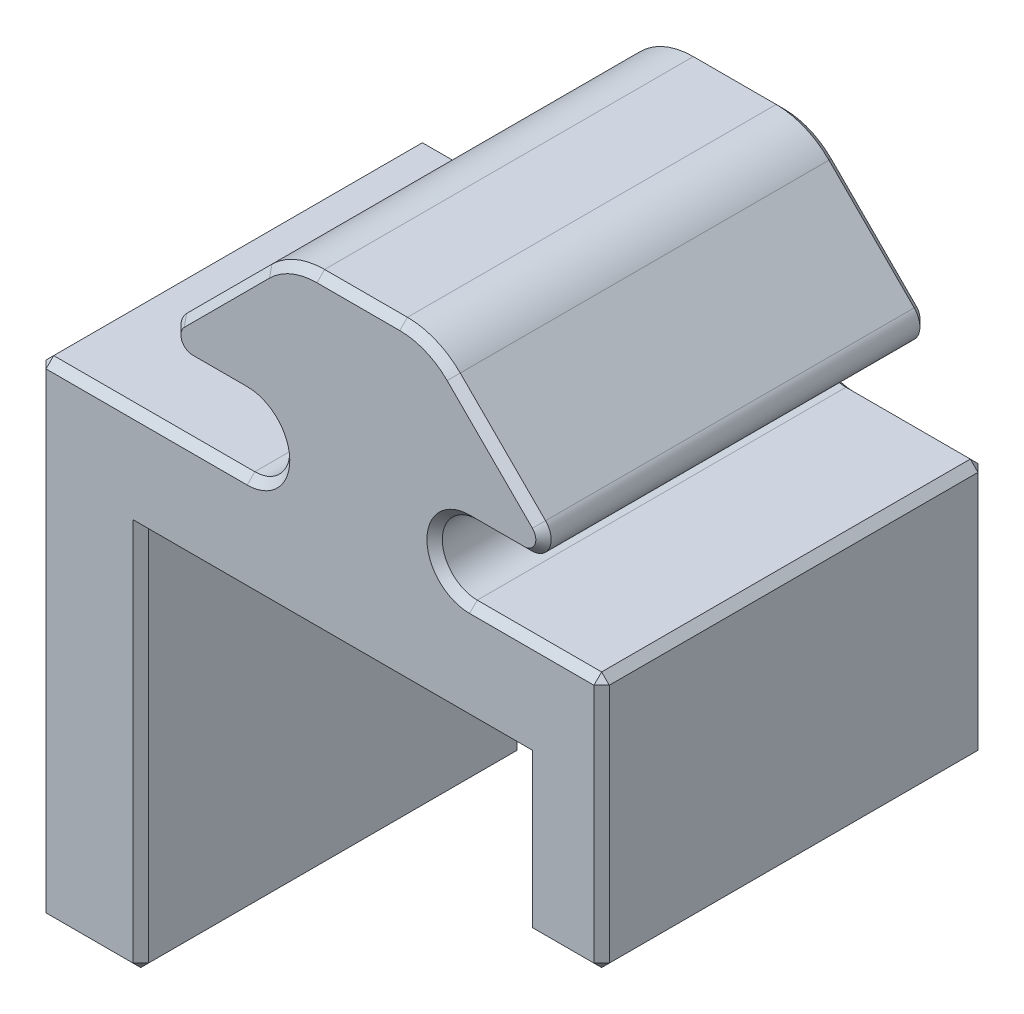
SolidWorks part; units mm, degrees
ref_plane "Front Plane" through (0, 0, 0) normal (0, 0, 1) x (1, 0, 0)
ref_plane "Top Plane" through (0, 0, 0) normal (0, 1, 0) x (1, 0, 0)
ref_plane "Right Plane" through (0, 0, 0) normal (1, 0, 0) x (0, 0, -1)
sketch "Sketch1" plane through (0, 0, 0) normal (0, 0, 1) x (1, 0, 0)
  line L0 (-5.3171, -3.1021) -> (-5.3171, -5.1021) construction
  line L1 (-5.3171, -5.1021) -> (5.3171, -5.1021) construction
  line L2 (5.3171, -5.1021) -> (5.3171, -3.1021) construction
  line L13 (-5.3171, -3.1021) -> (-4.3434, -3.1021) construction
  line L14 (-4.3434, -0.8923) -> (-6.4748, -0.8923) construction
  line L15 (-7.1932, 0.8421) -> (-3.8632, 4.1722) construction
  line L16 (-1.6181, 5.1021) -> (1.6181, 5.1021) construction
  line L17 (3.8632, 4.1722) -> (7.1932, 0.8421) construction
  line L18 (6.4748, -0.8923) -> (4.3434, -0.8923) construction
  line L19 (4.3434, -3.1021) -> (5.3171, -3.1021) construction
  line L20 (-5.0571, -3.3621) -> (-5.0571, -4.8421) construction
  line L21 (-5.0571, -4.8421) -> (5.0571, -4.8421) construction
  line L22 (5.0571, -4.8421) -> (5.0571, -3.3621) construction
  line L23 (4.3434, -3.3621) -> (5.0571, -3.3621)
  line L24 (6.4748, -0.6323) -> (4.3434, -0.6323)
  line L25 (3.6793, 3.9883) -> (7.0094, 0.6583)
  line L26 (-1.6181, 4.8421) -> (1.6181, 4.8421)
  line L27 (-7.0094, 0.6583) -> (-3.6793, 3.9883)
  line L28 (-4.3434, -0.6323) -> (-6.4748, -0.6323)
  line L29 (-5.0571, -3.3621) -> (-4.3434, -3.3621)
  line L30 (-5.0571, -3.3621) -> (-12.5, -3.3621)
  line L31 (-12.5, -3.3621) -> (-12.5, -7.3621)
  line L32 (-12.5, -7.3621) -> (9.5, -7.3621)
  line L33 (9.5, -7.3621) -> (9.5, -3.3621)
  line L34 (9.5, -3.3621) -> (5.0571, -3.3621)
  arc A6 (-4.3434, -3.1021) -> (-4.3434, -0.8923) centre (-4.3434, -1.9972) ccw construction
  arc A7 (-7.1932, 0.8421) -> (-6.4748, -0.8923) centre (-6.4748, 0.1237) ccw construction
  arc A8 (-1.6181, 5.1021) -> (-3.8632, 4.1722) centre (-1.6181, 1.9271) ccw construction
  arc A9 (3.8632, 4.1722) -> (1.6181, 5.1021) centre (1.6181, 1.9271) ccw construction
  arc A10 (6.4748, -0.8923) -> (7.1932, 0.8421) centre (6.4748, 0.1237) ccw construction
  arc A11 (4.3434, -0.8923) -> (4.3434, -3.1021) centre (4.3434, -1.9972) ccw construction
  arc A12 (4.3434, -0.6323) -> (4.3434, -3.3621) centre (4.3434, -1.9972) ccw
  arc A13 (6.4748, -0.6323) -> (7.0094, 0.6583) centre (6.4748, 0.1237) ccw
  arc A14 (3.6793, 3.9883) -> (1.6181, 4.8421) centre (1.6181, 1.9271) ccw
  arc A15 (-1.6181, 4.8421) -> (-3.6793, 3.9883) centre (-1.6181, 1.9271) ccw
  arc A16 (-7.0094, 0.6583) -> (-6.4748, -0.6323) centre (-6.4748, 0.1237) ccw
  arc A17 (-4.3434, -3.3621) -> (-4.3434, -0.6323) centre (-4.3434, -1.9972) ccw
  dimension "D1" = 0.26
  dimension "D2" = 4
  dimension "D3" = 12.5
  dimension "D4" = 22
extrude "Boss-Extrude1" add sketch "Sketch1" along normal blind 15
sketch "Sketch2" plane through (0, -7.3621, 0) normal (0, -1, 0) x (1, 0, 0)
  line L0 (-12.5, 15) -> (9.5, 15) construction
  line L1 (-12.5, 0) -> (-8.5, 0)
  line L2 (-12.5, 0) -> (-12.5, 15)
  line L3 (-12.5, 15) -> (-8.5, 15)
  line L4 (-8.5, 0) -> (-8.5, 15)
  dimension "D1" = 4
extrude "Boss-Extrude2" add sketch "Sketch2" along normal blind 15
sketch "Sketch3" plane through (0, -7.3621, 0) normal (0, -1, 0) x (1, 0, 0)
  line L0 (-8.5, 0) -> (9.5, 0) construction
  line L1 (9.5, 15) -> (6.5, 15)
  line L2 (9.5, 15) -> (9.5, 0)
  line L3 (9.5, 0) -> (6.5, 0)
  line L4 (6.5, 15) -> (6.5, 0)
  line L6 (-8.5, 0) -> (-8.5, 15) construction
  dimension "D1" = 15
extrude "Boss-Extrude3" add sketch "Sketch3" along normal blind 6
chamfer "Chamfer1" distance 0.3 angle 45 46 edges at (-10.5, -22.3621, 0) (-8.5, -14.8621, 0) (-1, -7.3621, 0) (6.5, -10.3621, 0) (8, -13.3621, 0) (9.5, -8.3621, 0) (6.9217, -3.3621, 0) (2.9785, -1.9972, 0) (5.4091, -0.6323, 0) (7.1732, -0.1656, 0) (5.3443, 2.3233, 0) (2.7336, 4.6202, 0) (0, 4.8421, 0) (-2.7336, 4.6202, 0) (-5.3443, 2.3233, 0) (-7.1732, -0.1656, 0) (-5.4091, -0.6323, 0) (-2.9785, -1.9972, 0) (-8.4217, -3.3621, 0) (-12.5, -12.8621, 0) (-2.9785, -1.9972, 15) (-5.4091, -0.6323, 15) (-7.1732, -0.1656, 15) (-5.3443, 2.3233, 15) (-2.7336, 4.6202, 15) (0, 4.8421, 15) (2.7336, 4.6202, 15) (5.3443, 2.3233, 15) (7.1732, -0.1656, 15) (5.4091, -0.6323, 15) (2.9785, -1.9972, 15) (6.9217, -3.3621, 15) (9.5, -8.3621, 15) (8, -13.3621, 15) (6.5, -10.3621, 15) (-1, -7.3621, 15) (-8.5, -14.8621, 15) (-10.5, -22.3621, 15) (-12.5, -12.8621, 15) (-8.4217, -3.3621, 15) (-12.5, -22.3621, 7.5) (-8.5, -22.3621, 7.5) (6.5, -13.3621, 7.5) (9.5, -13.3621, 7.5) (9.5, -3.3621, 7.5) (-12.5, -3.3621, 7.5)
